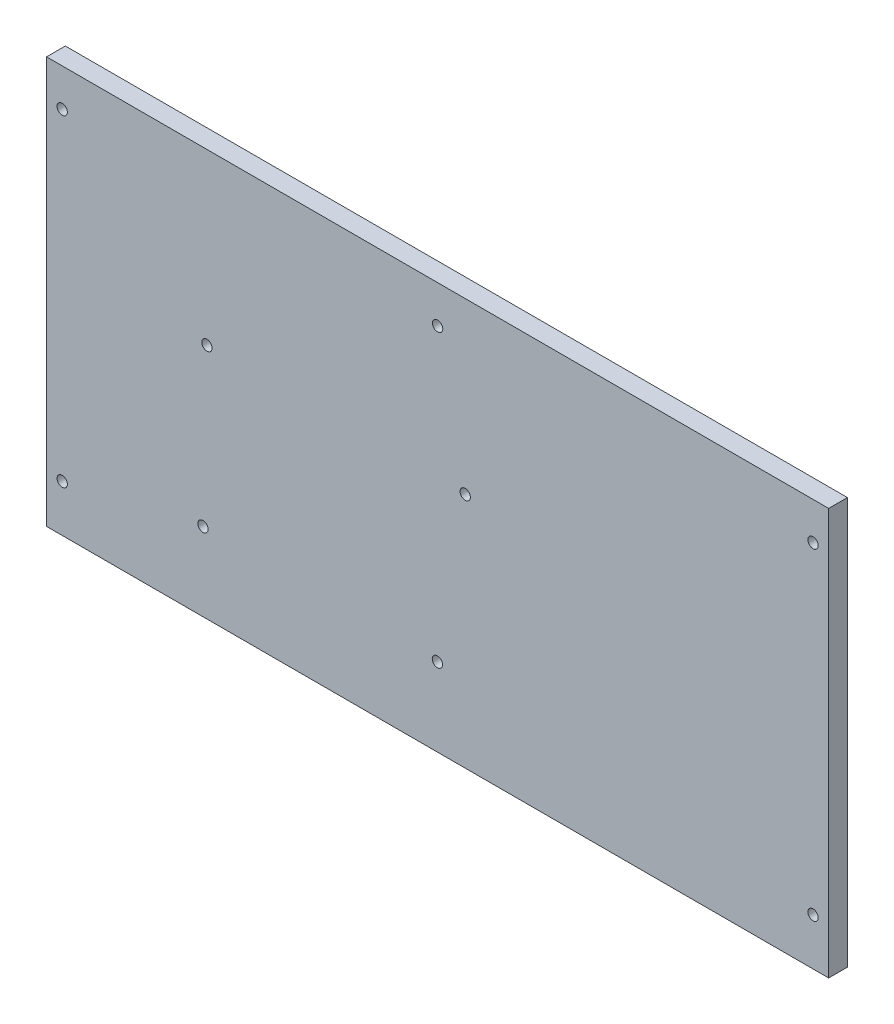
SolidWorks part; units mm, degrees
material "Balsa"
ref_plane "Plano frontal" through (0, 0, 0) normal (0, 0, 1) x (1, 0, 0)
ref_plane "Plano superior" through (0, 0, 0) normal (0, 1, 0) x (1, 0, 0)
ref_plane "Plano direito" through (0, 0, 0) normal (1, 0, 0) x (0, 0, -1)
sketch "Esboço1" plane through (0, 0, 0) normal (0, 0, 1) x (1, 0, 0)
  line L0 (0, 0) -> (0, 70.7174) construction
  line L1 (-125, 65) -> (125, 65)
  line L2 (-125, 65) -> (-125, -65)
  line L3 (-125, -65) -> (125, -65)
  line L4 (125, 65) -> (125, -65)
  line L5 (-125, 65) -> (125, -65) construction
  line L6 (-125, -65) -> (125, 65) construction
  circle A0 centre (-120, 53) radius 1.65
  circle A1 centre (-120, -50) radius 1.65
  circle A2 centre (0, 53) radius 1.65
  circle A3 centre (120, -50) radius 1.65
  circle A4 centre (120, 53) radius 1.65
  point P0 (0, 0)
  dimension "D1" = 3.3
  dimension "D2" = 250
  dimension "D3" = 130
  dimension "D4" = 12
  dimension "D5" = 5
  dimension "D6" = 103
extrude "Ressalto-extrusão1" add sketch "Esboço1" along normal blind 6
sketch "Esboço2" plane through (0, 0, 0) normal (0, 0, -1) x (-1, 0, 0)
  line L0 (125, -65) -> (-125, -65) construction
  line L1 (125, 65) -> (125, -65) construction
  line L6 (75, -40) -> (0.07, -40) construction
  line L7 (0.07, -40) -> (-8.82, 10.8) construction
  line L8 (-8.82, 10.8) -> (73.73, 10.8) construction
  circle A0 centre (73.73, 10.8) radius 1.65
  circle A1 centre (75, -40) radius 1.65
  circle A2 centre (0.07, -40) radius 1.65
  circle A3 centre (-8.82, 10.8) radius 1.65
  dimension "D5" = 3.3
  dimension "D1" = 82.55
  dimension "D2" = 50.8
  dimension "D3" = 74.93
  dimension "D4" = 1.27
  dimension "D6" = 25
  dimension "D7" = 50
extrude "Corte-extrusão1" cut sketch "Esboço2" against normal blind 6
